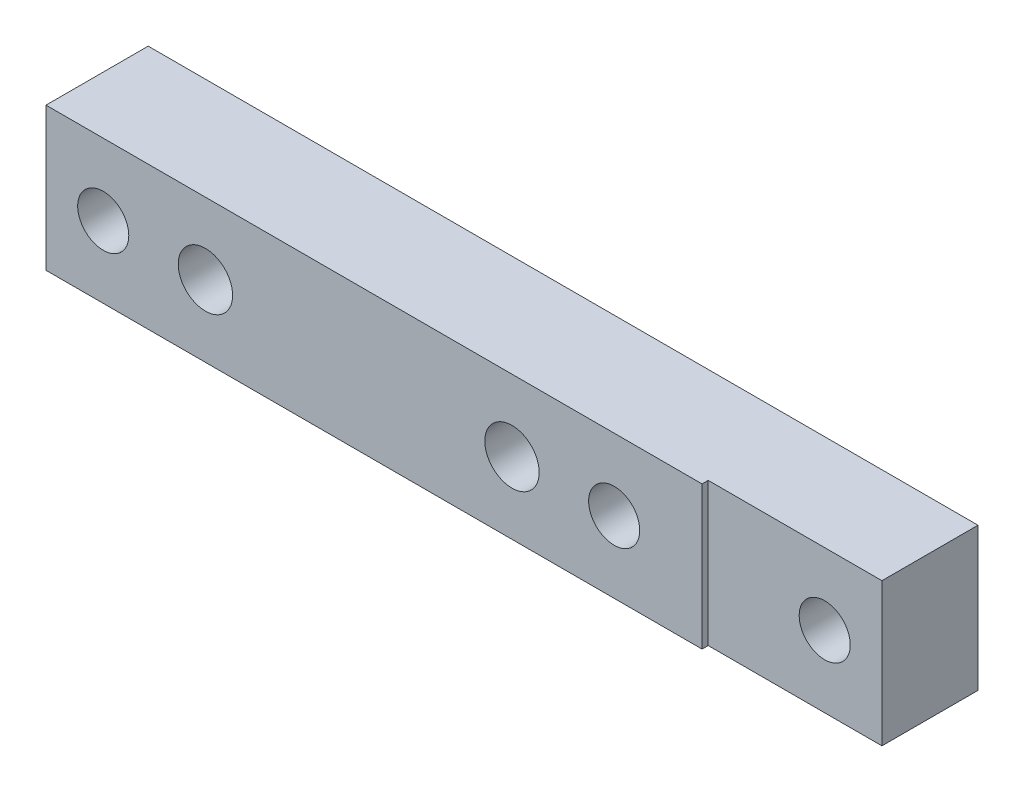
SolidWorks part; units mm, degrees
material "6061-T6 Al"
ref_plane "Front" through (0, 0, 0) normal (0, 0, 1) x (1, 0, 0)
ref_plane "Top" through (0, 0, 0) normal (0, 1, 0) x (1, 0, 0)
ref_plane "Right" through (0, 0, 0) normal (1, 0, 0) x (0, 0, -1)
sketch "Sketch" plane through (0, 0, 0) normal (0, 0, 1) x (1, 0, 0)
  line L2 (0, 0) -> (-12.7, 0) construction
  line L3 (-70.612, 8.89) -> (32.512, 8.89)
  line L4 (-70.612, 8.89) -> (-70.612, -8.89)
  line L6 (-70.612, -8.89) -> (32.512, -8.89)
  line L7 (32.512, 8.89) -> (32.512, 0)
  line L8 (-12.7, 0) -> (-50.8, 0) construction
  line L9 (-50.8, 0) -> (-63.5, 0) construction
  line L10 (32.512, 0) -> (32.512, -8.89)
  line L11 (0, 0) -> (25.4, 0) construction
  circle A0 centre (-63.5, 0) radius 3.175
  circle A2 centre (0, 0) radius 3.175
  circle A3 centre (25.4, 0) radius 3.175
  point P5 (-25.908, 20.828)
  point P6 (25.908, 20.828)
  point P7 (25.908, -20.828)
  point P8 (-25.908, -20.828)
  point P63 (-25.781, -19.05)
  point P64 (25.781, -19.05)
  dimension "D5" = 70.612
  dimension "D6" = 25.4
  dimension "D7" = 6.35
  dimension "D3" = 63.5
  dimension "D4" = 32.512
  dimension "D1" = 17.78
  dimension "D2" = 12.7
extrude "Boss-Extrude1" add sketch "Sketch" against normal blind 12.7
sketch "Sketch3" plane through (0, 0, 0) normal (0, 0, -1) x (-1, 0, 0)
  line L4 (70.612, -8.89) -> (70.612, 8.89)
  line L5 (70.612, 8.89) -> (-32.512, 8.89)
  line L6 (-32.512, 8.89) -> (-32.512, -8.89)
  line L7 (-32.512, -8.89) -> (70.612, -8.89)
  line L8 (-10.922, -8.89) -> (-10.922, 8.89)
  line L9 (-10.922, 8.89) -> (-32.512, 8.89)
  line L10 (-32.512, 8.89) -> (-32.512, -8.89)
  line L11 (-32.512, -8.89) -> (-10.922, -8.89)
  dimension "D2" = 10.922
  dimension "D1" = 0
extrude "Cut-Extrude1" cut sketch "Sketch3" along normal blind 0.762
hole_wizard "1/4 Clearance Hole1" positions "Sketch2" profile "Sketch1" hole size "1/4" standard "ANSI Inch" end condition up to next
sketch "Sketch2" plane through (0, 0, 0) normal (0, 0, 1) x (1, 0, 0)
  point P0 (-50.8, 0)
  point P3 (-12.7, 0)
sketch "Sketch1" plane through (-50.8, 0, 0) normal (1, 0, 0) x (0, -1, 0)
  line L0 (0, 0) -> (0, 12.7)
  line L1 (0, 12.7) -> (3.3782, 12.7)
  line L2 (3.3782, 12.7) -> (3.3782, 0)
  line L5 (3.3782, 0) -> (0, 0)
  line L11 (0, -6.35) -> (0, 107.95) construction
  dimension "Thru Hole Dia." = 6.7564
  dimension "Thru Hole Depth" = 12.7
